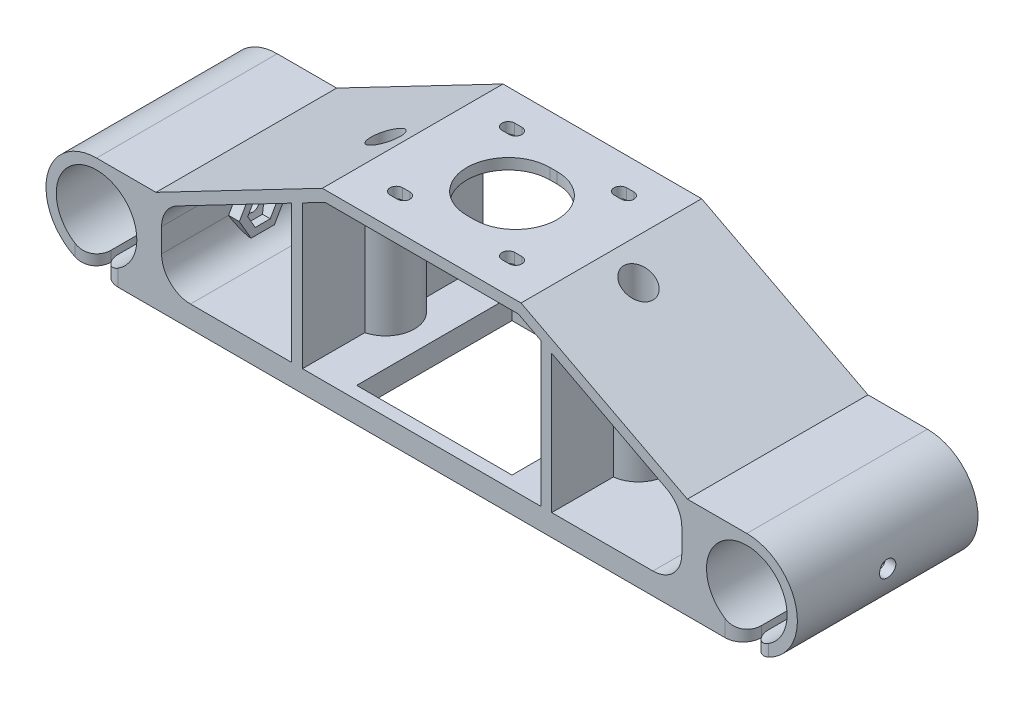
SolidWorks part; units mm, degrees
ref_plane "Front Plane" through (0, 0, 0) normal (0, 0, 1) x (1, 0, 0)
ref_plane "Top Plane" through (0, 0, 0) normal (0, 1, 0) x (1, 0, 0)
ref_plane "Right Plane" through (0, 0, 0) normal (1, 0, 0) x (0, 0, -1)
sketch "Sketch1" plane through (0, 0, 0) normal (0, 0, 1) x (1, 0, 0)
  line L0 (0, -14) -> (180, -14)
  line L1 (0, 14) -> (16.4571, 14)
  line L2 (18, 11.4212) -> (18, -8)
  line L3 (18, -8) -> (162, -8)
  line L4 (162, -8) -> (162, 11.4212)
  line L5 (163.5429, 14) -> (180, 14)
  line L6 (16.4571, 14) -> (62.5, 38)
  line L7 (62.5, 38) -> (117.5, 38)
  line L8 (117.5, 38) -> (163.5429, 14)
  line L9 (18, 11.4212) -> (63.235, 35)
  line L10 (63.235, 35) -> (116.765, 35)
  line L11 (116.765, 35) -> (162, 11.4212)
  line L14 (17.8437, 11.3397) -> (63.235, 35) construction
  line L15 (116.765, 35) -> (162.1563, 11.3397) construction
  circle A0 centre (0, 0) radius 11.15
  circle A1 centre (180, 0) radius 11.15
  arc A2 (0, 14) -> (0, -14) centre (0, 0) ccw
  arc A3 (180, -14) -> (180, 14) centre (180, 0) ccw
  dimension "D1" = 22.3
  dimension "D2" = 180
  dimension "D3" = 28
  dimension "D4" = 18
  dimension "D5" = 6
  dimension "D6" = 52
  dimension "D7" = 55
  dimension "D9" = 18
  dimension "D8" = 3
extrude "Boss-Extrude1" add sketch "Sketch1" along normal blind 50
sketch "Sketch2" plane through (0, 38, 0) normal (0, 1, 0) x (1, 0, 0)
  line L0 (90, 0) -> (90, -50) construction
  line L1 (117.5, 0) -> (62.5, 0) construction
  line L2 (117.5, -50) -> (62.5, -50) construction
  line L3 (89, -25) -> (91, -25) construction
  line L4 (89, -13.5) -> (91, -13.5)
  line L5 (89, -36.5) -> (91, -36.5)
  line L6 (90, -25) -> (74.5, -25) construction
  line L7 (74.5, -25) -> (74.5, -9.5) construction
  line L8 (74.5, -9.5) -> (105.5, -9.5) construction
  line L9 (105.5, -9.5) -> (105.5, -40.5) construction
  line L10 (105.5, -40.5) -> (74.5, -40.5) construction
  line L11 (73.5, -9.5) -> (75.5, -9.5) construction
  line L12 (73.5, -7.75) -> (75.5, -7.75)
  line L13 (73.5, -11.25) -> (75.5, -11.25)
  line L14 (104.5, -9.5) -> (106.5, -9.5) construction
  line L15 (104.5, -7.75) -> (106.5, -7.75)
  line L16 (104.5, -11.25) -> (106.5, -11.25)
  line L17 (104.5, -40.5) -> (106.5, -40.5) construction
  line L18 (104.5, -38.75) -> (106.5, -38.75)
  line L19 (104.5, -42.25) -> (106.5, -42.25)
  line L20 (73.5, -40.5) -> (75.5, -40.5) construction
  line L21 (73.5, -38.75) -> (75.5, -38.75)
  line L22 (73.5, -42.25) -> (75.5, -42.25)
  arc A0 (89, -13.5) -> (89, -36.5) centre (89, -25) ccw
  arc A1 (91, -36.5) -> (91, -13.5) centre (91, -25) ccw
  arc A2 (73.5, -7.75) -> (73.5, -11.25) centre (73.5, -9.5) ccw
  arc A3 (75.5, -11.25) -> (75.5, -7.75) centre (75.5, -9.5) ccw
  arc A4 (104.5, -7.75) -> (104.5, -11.25) centre (104.5, -9.5) ccw
  arc A5 (106.5, -11.25) -> (106.5, -7.75) centre (106.5, -9.5) ccw
  arc A6 (104.5, -38.75) -> (104.5, -42.25) centre (104.5, -40.5) ccw
  arc A7 (106.5, -42.25) -> (106.5, -38.75) centre (106.5, -40.5) ccw
  arc A8 (73.5, -38.75) -> (73.5, -42.25) centre (73.5, -40.5) ccw
  arc A9 (75.5, -42.25) -> (75.5, -38.75) centre (75.5, -40.5) ccw
  point P8 (90, -25)
  point P15 (90, -9.5)
  point P22 (74.5, -9.5)
  point P32 (105.5, -9.5)
  point P39 (105.5, -40.5)
  point P46 (74.5, -40.5)
  dimension "D1" = 11.5
  dimension "D5" = 1.75
  dimension "D2" = 2
  dimension "D3" = 31
  dimension "D4" = 15.5
  dimension "D6" = 2
  dimension "D7" = 2
  dimension "D8" = 2
extrude "Cut-Extrude1" cut sketch "Sketch2" against normal blind 26
sketch "Sketch3" plane through (0, -8, 0) normal (0, 1, 0) x (1, 0, 0)
  line L0 (90, 0) -> (90, -50) construction
  line L1 (18, 0) -> (162, 0) construction
  line L2 (18, -50) -> (162, -50) construction
  line L4 (68.5, -3.5) -> (111.5, -3.5)
  line L5 (68.5, -3.5) -> (68.5, -46.5)
  line L6 (68.5, -46.5) -> (111.5, -46.5)
  line L7 (111.5, -3.5) -> (111.5, -46.5)
  line L8 (68.5, -3.5) -> (111.5, -46.5) construction
  line L9 (68.5, -46.5) -> (111.5, -3.5) construction
  point P6 (90, -25)
  dimension "D1" = 43
extrude "Cut-Extrude2" cut sketch "Sketch3" against normal blind 26
sketch "Sketch4" plane through (0, -8, 0) normal (0, 1, 0) x (1, 0, 0)
  line L0 (90, -13.5) -> (90, -36.5) construction
  line L1 (91, -13.5) -> (89, -13.5) construction
  line L2 (89, -36.5) -> (91, -36.5) construction
  line L3 (90, -25) -> (55, -25) construction
  line L4 (90, -25) -> (125, -25) construction
  line L5 (90, -36.5) -> (90, -46.5) construction
  line L6 (68.5, -46.5) -> (111.5, -46.5) construction
  circle A0 centre (55, -25) radius 8
  circle A1 centre (125, -25) radius 8
  dimension "D3" = 16
  dimension "D1" = 35
  dimension "D2" = 35
extrude "Boss-Extrude3" add sketch "Sketch4" along normal up to body
sketch "Sketch5" plane through (0, 38, 0) normal (0, 1, 0) x (1, 0, 0)
  circle A0 centre (55, -25) radius 4.05
  circle A1 centre (125, -25) radius 4.05
  dimension "D1" = 8.1
extrude "Cut-Extrude3" cut sketch "Sketch5" against normal offset from surface (43 mm away) 3 up to face at (125, -8, 33)
ref_plane "Plane1" through (90, 0, 0) normal (1, 0, 0) x (0, 0, -1)
ref_plane "Plane2" through (123, 0, 0) normal (1, 0, 0) x (0, 0, -1)
sketch "Sketch6" plane through (123, 0, 0) normal (1, 0, 0) x (0, 0, -1)
  line L0 (-32.746, -8) -> (-32.746, 31.75)
  line L1 (-17.254, 31.75) -> (-17.254, -8)
  line L2 (-17.254, 31.75) -> (-17.254, -8)
  line L3 (-32.746, -8) -> (-32.746, 31.75)
  line L4 (-50, 31.75) -> (-32.746, 31.75)
  line L5 (-17.254, 31.75) -> (0, 31.75)
  line L6 (-17.254, 31.75) -> (0, 31.75)
  line L7 (-50, 31.75) -> (-32.746, 31.75)
  line L8 (0, -8) -> (-17.254, -8)
  line L9 (-32.746, -8) -> (-50, -8)
  line L10 (-32.746, -8) -> (-50, -8)
  line L11 (0, -8) -> (-17.254, -8)
  line L12 (-50, 27.3897) -> (-50, -8)
  line L13 (0, 27.3897) -> (0, -8)
  line L15 (-50, 31.75) -> (-50, 27.3897)
  line L16 (0, 31.75) -> (0, 27.3897)
sketch "Sketch7" plane through (0, -14, 0) normal (0, -1, 0) x (-1, 0, 0)
  line L0 (-68.5, -25) -> (0, -25) construction
  line L1 (-68.5, -3.5) -> (-68.5, -46.5) construction
  line L2 (0, -50) -> (0, 0) construction
  line L3 (-68.5, -46.5) -> (-111.5, -46.5) construction
  line L4 (-10, -46.5) -> (-58.5, -46.5)
  line L5 (-5, -41.5) -> (-5, -8.5)
  line L6 (-10, -3.5) -> (-58.5, -3.5)
  line L7 (-63.5, -41.5) -> (-63.5, -8.5)
  line L8 (-5, -46.5) -> (-63.5, -3.5) construction
  line L9 (-5, -3.5) -> (-63.5, -46.5) construction
  arc A0 (-5, -8.5) -> (-10, -3.5) centre (-10, -8.5) ccw
  arc A1 (-58.5, -3.5) -> (-63.5, -8.5) centre (-58.5, -8.5) ccw
  arc A2 (-58.5, -46.5) -> (-63.5, -41.5) centre (-58.5, -41.5) cw
  arc A3 (-10, -46.5) -> (-5, -41.5) centre (-10, -41.5) ccw
  point P6 (-34.25, -25)
  dimension "D2" = 5
  dimension "D1" = 5
extrude "Cut-Extrude4" cut sketch "Sketch7" against normal blind 3
mirror "Mirror2" about plane through (90, 0, 0) normal (1, 0, 0) of "Cut-Extrude4"
fillet "Fillet1" radius 8 4 edges at (162, 11.4212, 25) (18, 11.4212, 25) (162, -8, 25) (18, -8, 25)
extrude "Boss-Extrude4" add sketch "Sketch6" along normal blind 3
mirror "Mirror3" about plane through (90, 0, 0) normal (1, 0, 0) of "Boss-Extrude4"
ref_plane "Plane3" through (180, 0, 0) normal (-1, 0, 0) x (0, 0, 1)
sketch "Sketch8" plane through (180, 0, 0) normal (-1, 0, 0) x (0, 0, 1)
  line L0 (0, 11.15) -> (50, 11.15)
  line L1 (50, -11.15) -> (0, -11.15)
  line L2 (50, -11.15) -> (0, -11.15)
  line L3 (0, 11.15) -> (50, 11.15)
  line L4 (25, 11.15) -> (25, -11.15) construction
  circle A0 centre (25, 0) radius 2.25
  dimension "D1" = 4.5
extrude "Cut-Extrude5" cut sketch "Sketch8" against normal blind 33 and the other way blind 44 contours A0
sketch "Sketch9" plane through (162, 0, 0) normal (-1, 0, 0) x (0, 0, 1)
  line L1 (20.8431, 0) -> (22.9215, -3.6)
  line L2 (22.9215, -3.6) -> (27.0785, -3.6)
  line L3 (27.0785, -3.6) -> (29.1569, 0)
  line L4 (29.1569, 0) -> (27.0785, 3.6)
  line L5 (27.0785, 3.6) -> (22.9215, 3.6)
  line L6 (22.9215, 3.6) -> (20.8431, 0)
  line L7 (18.5337, 0) -> (21.7668, -5.6)
  line L8 (21.7668, -5.6) -> (28.2332, -5.6)
  line L9 (28.2332, -5.6) -> (31.4663, 0)
  line L10 (31.4663, 0) -> (28.2332, 5.6)
  line L11 (28.2332, 5.6) -> (21.7668, 5.6)
  line L12 (21.7668, 5.6) -> (18.5337, 0)
  circle A0 centre (25, 0) radius 3.6 construction
  circle A1 centre (25, 0) radius 5.6 construction
  dimension "D1" = 7.2
  dimension "D2" = 2
extrude "Boss-Extrude5" add sketch "Sketch9" along normal blind 3
mirror "Mirror4" about plane through (90, 0, 0) normal (1, 0, 0) of "Boss-Extrude5", "Cut-Extrude5"
sketch "Sketch10" plane through (0, -14, 0) normal (0, -1, 0) x (-1, 0, 0)
  line L0 (0, 0) -> (0, -50)
extrude "Cut-Extrude-Thin1" cut sketch "Sketch10" against normal blind 10 and the other way through all thin thin type mid plane wall 2
mirror "Mirror5" about plane through (90, 0, 0) normal (1, 0, 0) of "Cut-Extrude-Thin1"
fillet "Fillet2" radius 5 8 edges at (181, -12.5347, 50) (181, -12.5347, 0) (179, -12.5525, 0) (179, -12.5525, 50) (1, -12.5525, 50) (1, -12.5525, 0) (-1, -12.5347, 0) (-1, -12.5347, 50)
